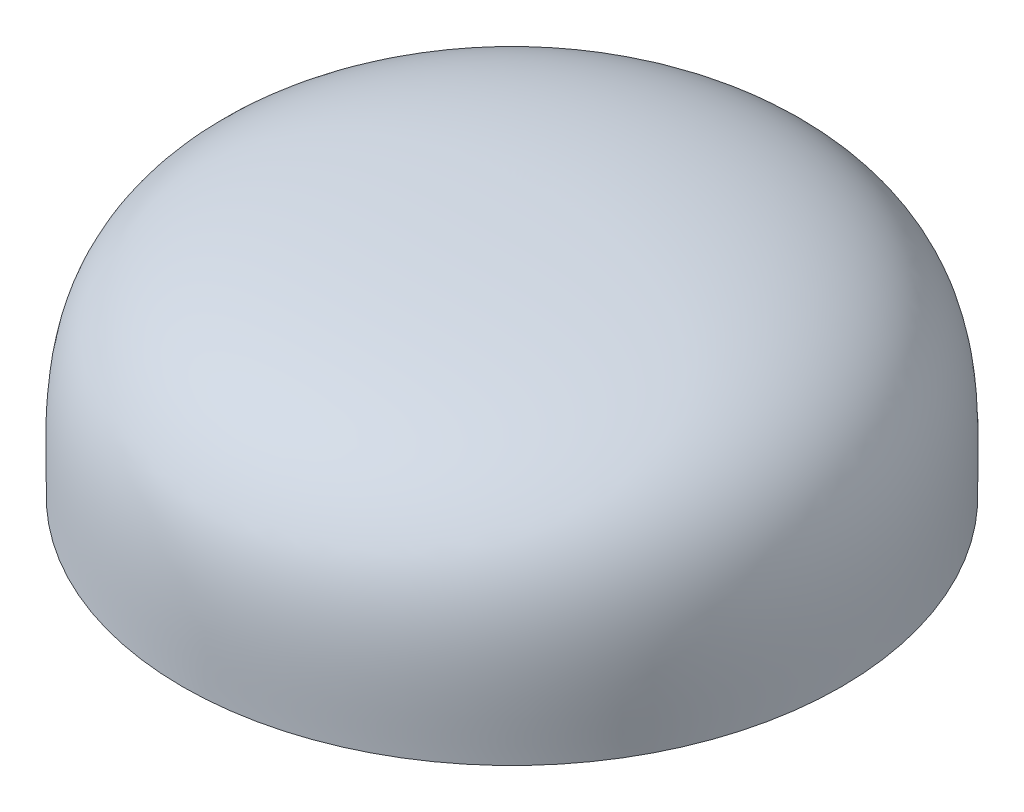
SolidWorks part; units mm, degrees
ref_plane "Front Plane" through (0, 0, 0) normal (0, 0, 1) x (1, 0, 0)
ref_plane "Top Plane" through (0, 0, 0) normal (0, 1, 0) x (1, 0, 0)
ref_plane "Right Plane" through (0, 0, 0) normal (1, 0, 0) x (0, 0, -1)
sketch "Sketch1" plane through (0, 0, 0) normal (0, 0, 1) x (1, 0, 0)
  line L0 (-1.5, 0) -> (-6.5, 0)
  line L1 (0, 0) -> (-1.5, 0) construction
  line L2 (0, 0) -> (0, 3) construction
  line L3 (0, 3) -> (-1.5, 3)
  line L4 (-1.5, 0) -> (-1.5, 3)
  line L5 (0, 3) -> (0, 5)
  spline S0 degree 3 poles (0, 5) (-6.9638, 5) (-6.5, 2.4594) (-6.5, 0) knots 0 0 0 0 1 1 1 1
  dimension "D1" = 1.5
  dimension "D2" = 3
  dimension "D3" = 5
  dimension "D4" = 2
revolve "Revolve1" add sketch "Sketch1" angle 360 about L5
